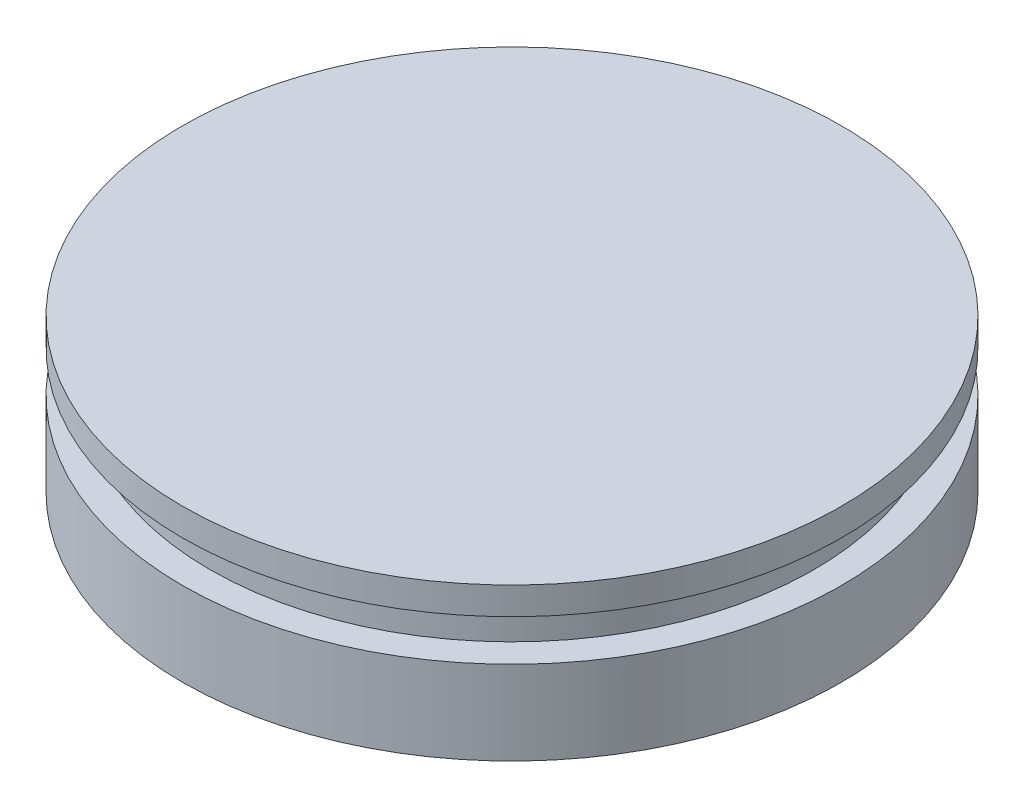
SolidWorks part; units mm, degrees
material "Silicon Rubber"
ref_plane "Front Plane" through (0, 0, 0) normal (0, 0, 1) x (1, 0, 0)
ref_plane "Top Plane" through (0, 0, 0) normal (0, 1, 0) x (1, 0, 0)
ref_plane "Right Plane" through (0, 0, 0) normal (1, 0, 0) x (0, 0, -1)
sketch "Sketch1" plane through (0, 0, 0) normal (0, 0, 1) x (1, 0, 0)
  line L3 (0, 50.358) -> (0, -222.3667) construction
  line L16 (-69.85, 1876.044) -> (-69.85, 1866.519)
  line L17 (-69.85, 1876.044) -> (-76.2, 1876.044)
  line L18 (-76.2, 1876.044) -> (-76.2, 1882.394)
  line L19 (-76.2, 1882.394) -> (0, 1882.394)
  line L20 (-69.85, 1866.519) -> (-76.2, 1866.519)
  line L24 (0, 1882.394) -> (0, 1869.694)
  line L25 (-76.2, 1847.1312) -> (-76.2, 1866.519)
  arc A2 (-76.2, 1847.1312) -> (0, 1869.694) centre (0, 1729.74) cw
  dimension "D6" = 9.525
  dimension "D1" = 139.954
  dimension "D2" = 76.2
  dimension "D3" = 12.7
  dimension "D4" = 6.35
  dimension "D8" = 6.35
  dimension "D10" = 6.35
revolve "Revolve1" add sketch "Sketch1" angle 360 about L3
equation "\"OD\"=5.25"
equation "\"t_wrap\"=0.131"
equation "\"t_wall\"=0.511"
